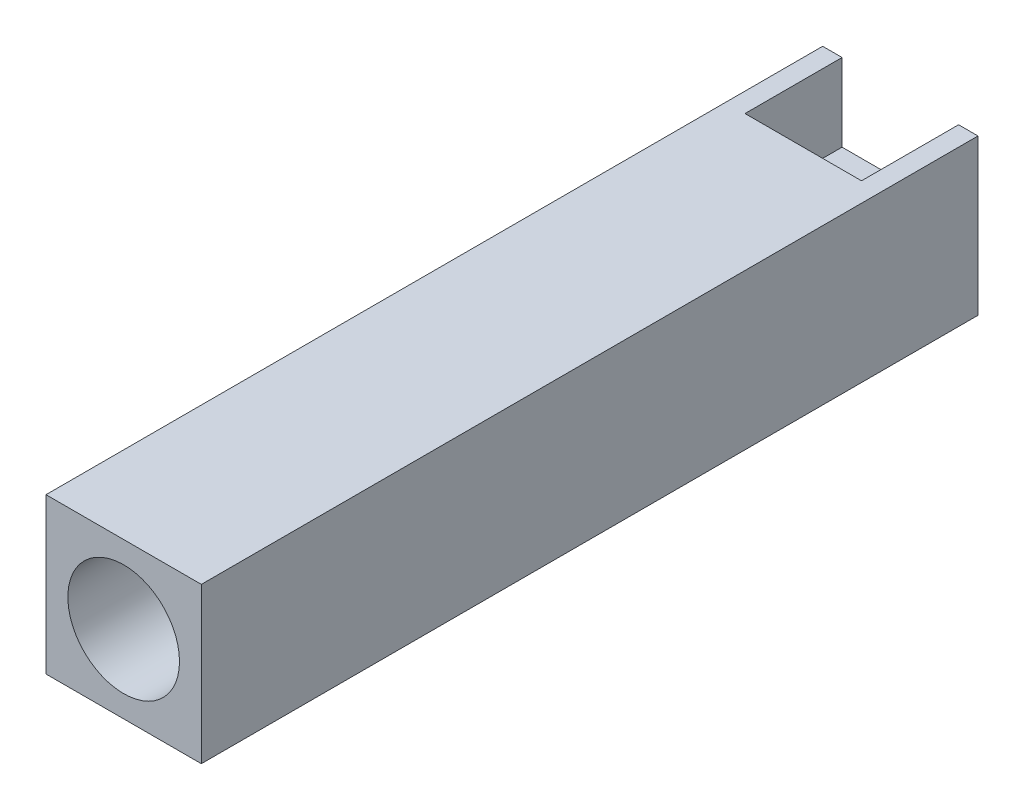
SolidWorks part; units mm, degrees
ref_plane "前视基准面" through (0, 0, 0) normal (0, 0, 1) x (1, 0, 0)
ref_plane "上视基准面" through (0, 0, 0) normal (0, 1, 0) x (1, 0, 0)
ref_plane "右视基准面" through (0, 0, 0) normal (1, 0, 0) x (0, 0, -1)
other "Configuration Table"
sketch "草图1" plane through (0, 0, 0) normal (0, 0, 1) x (1, 0, 0)
  line L1 (0, 0) -> (16, 0)
  line L2 (0, 0) -> (0, -16)
  line L3 (0, -16) -> (16, -16)
  line L4 (16, 0) -> (16, -16)
  line L5 (0, 0) -> (16, -16) construction
  line L6 (0, -16) -> (16, 0) construction
  point P4 (8, -8)
  dimension "D1" = 16
  dimension "D2" = 16
extrude "凸台-拉伸1" add sketch "草图1" along normal blind 80
sketch "草图2" plane through (0, 0, 80) normal (0, 0, 1) x (1, 0, 0)
  line L0 (0, 0) -> (16, -16) construction
  circle A0 centre (8, -8) radius 5.75
  dimension "D1" = 11.5
extrude "切除-拉伸1" cut sketch "草图2" against normal blind 50
sketch "草图10" plane through (0, 0, 0) normal (0, 0, -1) x (-1, 0, 0)
  line L0 (-14, -8) -> (-14, -13) construction
  line L1 (-16, 0) -> (0, 0) construction
  line L2 (-16, 0) -> (-16, -16) construction
  line L3 (-16, -16) -> (0, -16) construction
  line L4 (0, 0) -> (0, -16) construction
  line L5 (-16, 0) -> (0, -16) construction
  line L6 (-16, -16) -> (0, 0) construction
  line L7 (-14, 0) -> (-2, 0)
  line L8 (-14, 0) -> (-14, -8)
  line L9 (-14, -8) -> (-2, -8)
  line L10 (-2, 0) -> (-2, -8)
  line L11 (-14, 0) -> (-2, -8) construction
  line L12 (-14, -8) -> (-2, 0) construction
  line L14 (-14, -13) -> (-2, -13)
  line L15 (-14, -13) -> (-14, -16)
  line L16 (-14, -16) -> (-2, -16)
  line L17 (-2, -13) -> (-2, -16)
  line L18 (-14, -13) -> (-2, -16) construction
  line L19 (-14, -16) -> (-2, -13) construction
  point P4 (-8, -8)
  point P11 (-8, -4)
  point P16 (-8, -14.5)
  dimension "D1" = 2
  dimension "D2" = 2
  dimension "D3" = 8
  dimension "D4" = 5
extrude "切除-拉伸2" cut sketch "草图10" against normal blind 10
sketch "草图11" plane through (0, -13, 0) normal (0, -1, 0) x (1, 0, 0)
  line L1 (2, 10) -> (14, 10) construction
  line L2 (2, 10) -> (2, 0) construction
  line L3 (2, 0) -> (14, 0) construction
  line L4 (14, 10) -> (14, 0) construction
  line L5 (2, 10) -> (14, 0) construction
  line L6 (2, 0) -> (14, 10) construction
  circle A0 centre (8, 5) radius 3.25
  point P4 (8, 5)
  dimension "D1" = 6.5
extrude "切除-拉伸5" cut sketch "草图11" against normal blind 1
hole_wizard "M4 螺纹孔的螺纹孔钻头1" positions "草图12" profile "草图13" hole size "M4" standard "ISO" end condition up to next
sketch "草图12" plane through (0, -12, 0) normal (0, -1, 0) x (-1, 0, 0)
  point P0 (-8, -5)
sketch "草图13" plane through (8, -12, 5) normal (1, 0, 0) x (0, 0, -1)
  line L0 (0, 0) -> (0, 4)
  line L1 (0, 4) -> (1.65, 4)
  line L2 (1.65, 4) -> (1.65, 0)
  line L5 (1.65, 0) -> (0, 0)
  line L11 (0, -6.35) -> (0, 107.95) construction
  dimension "通孔孔直径" = 3.3
  dimension "通孔孔深度" = 4
